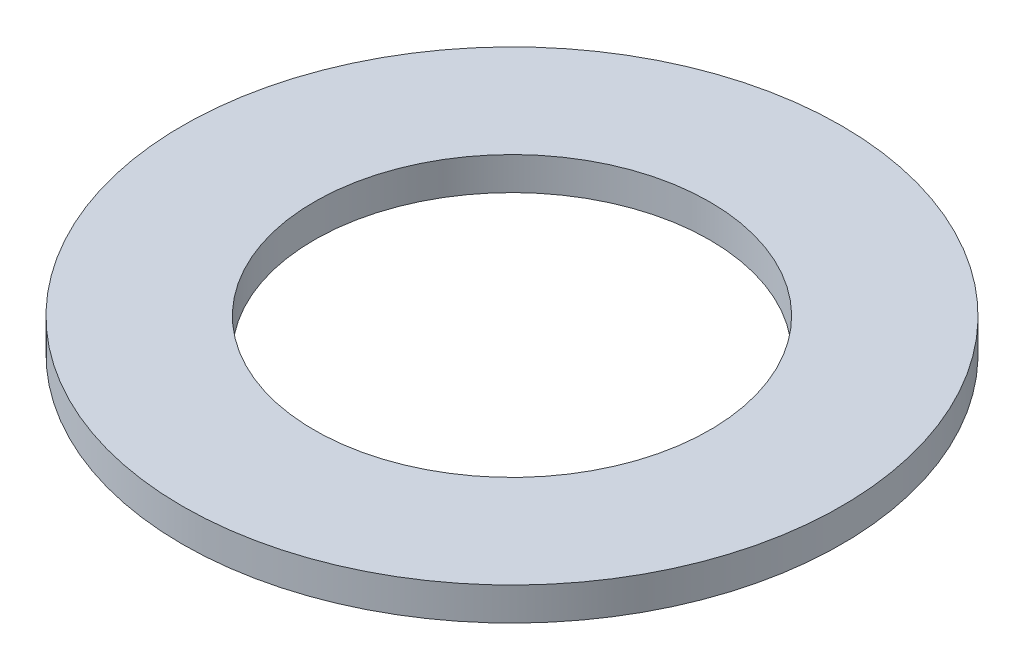
SolidWorks part; units mm, degrees
ref_plane "Front Plane" through (0, 0, 0) normal (0, 0, 1) x (1, 0, 0)
ref_plane "Top Plane" through (0, 0, 0) normal (0, 1, 0) x (1, 0, 0)
ref_plane "Right Plane" through (0, 0, 0) normal (1, 0, 0) x (0, 0, -1)
sketch "Sketch1" plane through (0, 0, 0) normal (0, 0, 1) x (1, 0, 0)
  line L0 (0, 0) -> (0, 4.1899) construction
  line L2 (-2.3813, 0) -> (-3.9688, 0)
  line L3 (-2.3813, 0) -> (-2.3813, 0.3969)
  line L4 (-2.3813, 0.3969) -> (-3.9688, 0.3969)
  line L5 (-3.9688, 0) -> (-3.9688, 0.3969)
  dimension "D1" = 0.3969
  dimension "D2" = 4.7625
  dimension "D3" = 7.9375
revolve "Revolve1" add sketch "Sketch1" angle 360 about L0
